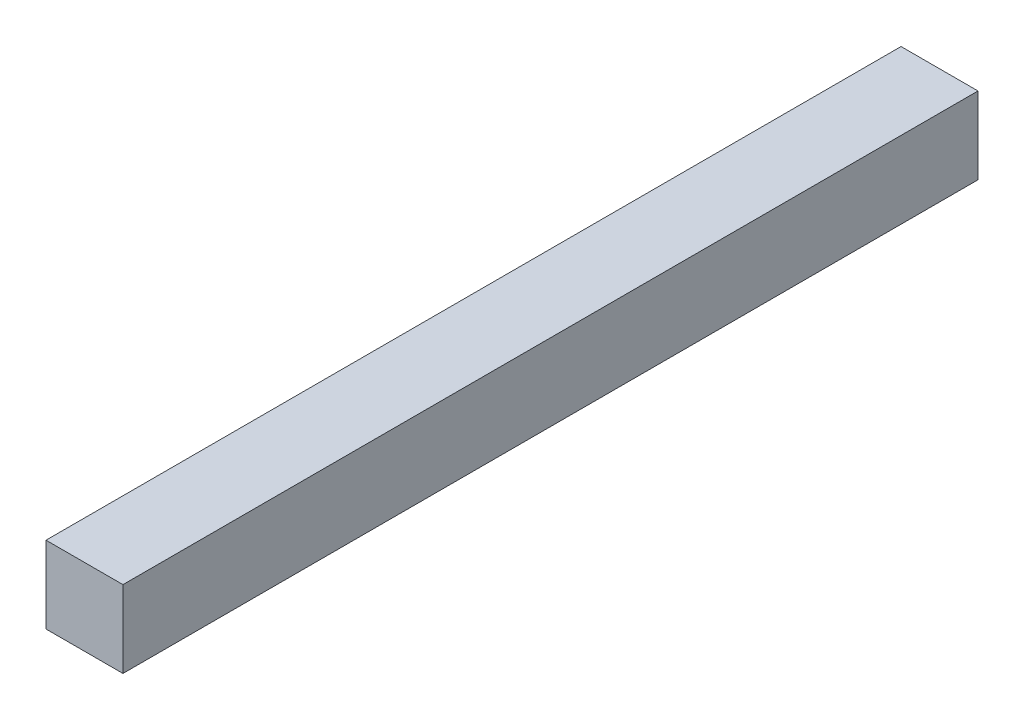
SolidWorks part; units mm, degrees
ref_plane "Front Plane" through (0, 0, 0) normal (0, 0, 1) x (1, 0, 0)
ref_plane "Top Plane" through (0, 0, 0) normal (0, 1, 0) x (1, 0, 0)
ref_plane "Right Plane" through (0, 0, 0) normal (1, 0, 0) x (0, 0, -1)
sketch "Sketch1" plane through (0, 0, 0) normal (0, 0, 1) x (1, 0, 0)
  line L1 (0, 0) -> (45, 0)
  line L2 (0, 0) -> (0, 45)
  line L3 (0, 45) -> (45, 45)
  line L4 (45, 0) -> (45, 45)
  dimension "D1" = 45
  dimension "D2" = 45
extrude "Boss-Extrude1" add sketch "Sketch1" along normal blind 500
